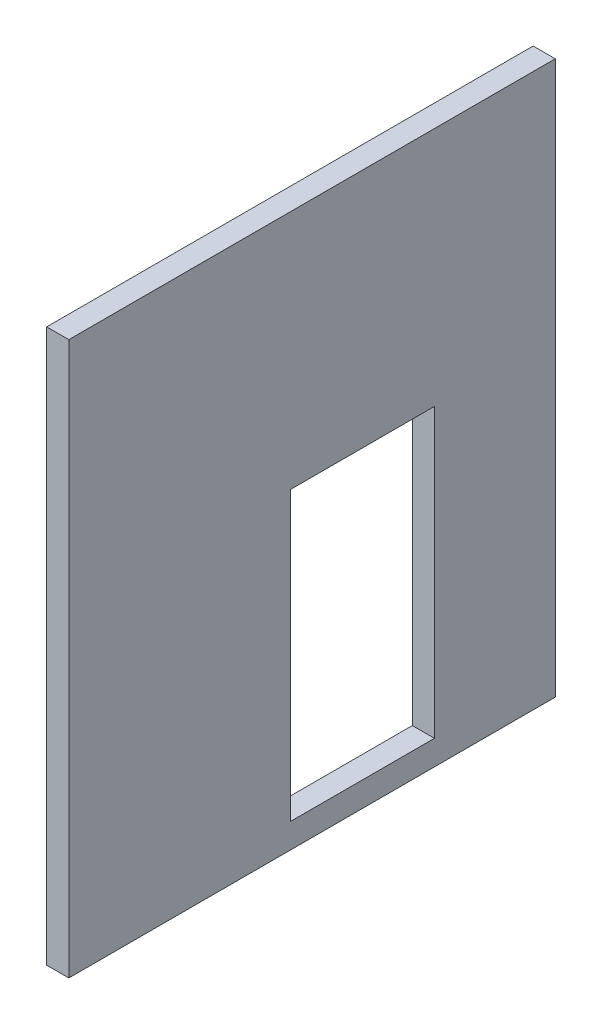
SolidWorks part; units mm, degrees
material "Teck"
ref_plane "Plan de face" through (0, 0, 0) normal (0, 0, 1) x (1, 0, 0)
ref_plane "Plan de dessus" through (0, 0, 0) normal (0, 1, 0) x (1, 0, 0)
ref_plane "Plan de droite" through (0, 0, 0) normal (1, 0, 0) x (0, 0, -1)
sketch "Esquisse1" plane through (0, 0, 0) normal (1, 0, 0) x (0, 0, -1)
  line L1 (-220, -250) -> (220, -250)
  line L2 (-220, -250) -> (-220, 250)
  line L3 (-220, 250) -> (220, 250)
  line L4 (220, -250) -> (220, 250)
  line L5 (-220, -250) -> (220, 250) construction
  line L6 (-220, 250) -> (220, -250) construction
  point P0 (0, 0)
  dimension "D1" = 440
  dimension "D2" = 500
extrude "Boss.-Extru.1" add sketch "Esquisse1" along normal blind 20
sketch "Esquisse3" plane through (20, 0, 0) normal (1, 0, 0) x (0, 0, -1)
  line L1 (110.6643, -227.619) -> (-19.3357, -227.619)
  line L2 (110.6643, -227.619) -> (110.6643, 32.381)
  line L3 (110.6643, 32.381) -> (-19.3357, 32.381)
  line L4 (-19.3357, -227.619) -> (-19.3357, 32.381)
  dimension "D1" = 260
  dimension "D2" = 130
extrude "Enlèv. mat.-Extru.1" cut sketch "Esquisse3" against normal blind 20
